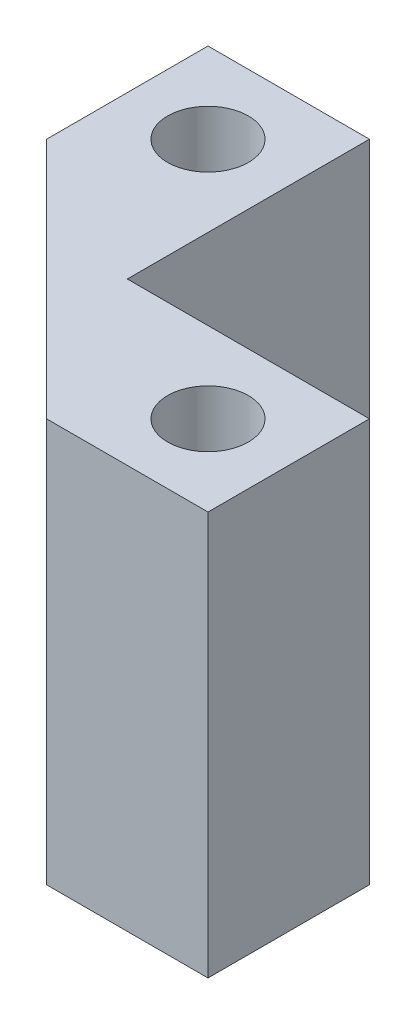
SolidWorks part; units mm, degrees
ref_plane "Front Plane" through (0, 0, 0) normal (0, 0, 1) x (1, 0, 0)
ref_plane "Top Plane" through (0, 0, 0) normal (0, 1, 0) x (1, 0, 0)
ref_plane "Right Plane" through (0, 0, 0) normal (1, 0, 0) x (0, 0, -1)
sketch "Sketch1" plane through (0, 0, 0) normal (0, 1, 0) x (1, 0, 0)
  line L7 (5, 5) -> (5, 20)
  line L8 (5, 5) -> (20, 5)
  line L9 (5, 20) -> (-5, 20)
  line L10 (20, 5) -> (20, -5)
  line L11 (20, -5) -> (10, -5)
  line L12 (-5, 20) -> (-5, 10)
  line L13 (-5, 10) -> (10, -5)
  circle A2 centre (0, 15) radius 2.5
  circle A3 centre (15, 0) radius 2.5
  point P0 (0, 15)
  point P1 (15, 0)
  point P7 (5, 5)
  point P14 (0, 0)
  point P35 (-5, -5)
extrude "Boss-Extrude1" add sketch "Sketch1" along normal blind 25
